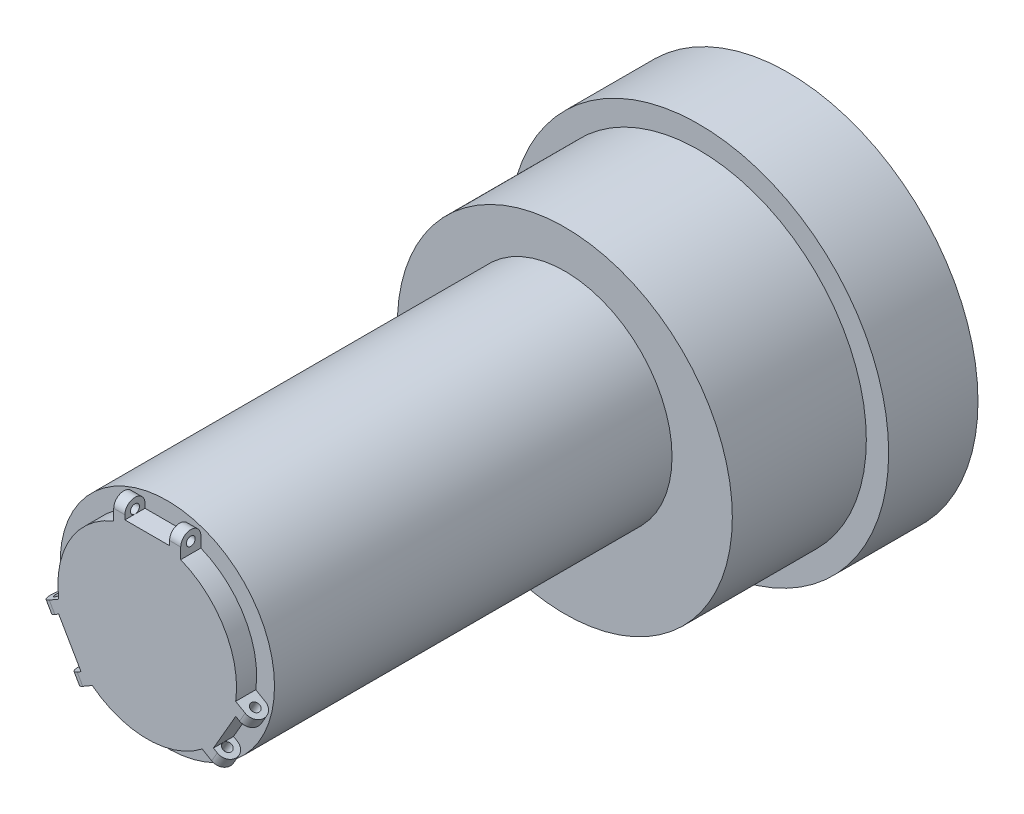
SolidWorks part; units mm, degrees
ref_plane "正面" through (0, 0, 0) normal (0, 0, 1) x (1, 0, 0)
ref_plane "平面" through (0, 0, 0) normal (0, 1, 0) x (1, 0, 0)
ref_plane "右側面" through (0, 0, 0) normal (1, 0, 0) x (0, 0, -1)
sketch "ｽｹｯﾁ1" plane through (0, 0, 0) normal (0, 0, 1) x (1, 0, 0)
  circle A0 centre (0, 0) radius 42.5
  dimension "D1" = 85
extrude "ﾎﾞｽ - 押し出し1" add sketch "ｽｹｯﾁ1" along normal blind 20
sketch "ｽｹｯﾁ2" plane through (0, 0, 20) normal (0, 0, 1) x (1, 0, 0)
  circle A0 centre (0, 0) radius 37.5
  dimension "D1" = 75
extrude "ﾎﾞｽ - 押し出し2" add sketch "ｽｹｯﾁ2" along normal blind 30
sketch "ｽｹｯﾁ3" plane through (0, 0, 50) normal (0, 0, 1) x (1, 0, 0)
  line L0 (0, 5) -> (0, 0) construction
  line L1 (0, 29) -> (0, 37.5) construction
  circle A0 centre (0, 5) radius 24
  circle A1 centre (0, 0) radius 37.5 construction
  dimension "D2" = 48
  dimension "D1" = 8.5
extrude "ﾎﾞｽ - 押し出し3" add sketch "ｽｹｯﾁ3" along normal blind 89
sketch "ｽｹｯﾁ5" plane through (0, 0, 139) normal (0, 0, 1) x (1, 0, 0)
  circle A0 centre (0, 5) radius 20
  circle A1 centre (0, 5) radius 24 construction
  dimension "D1" = 40
extrude "ﾎﾞｽ - 押し出し4" add sketch "ｽｹｯﾁ5" along normal blind 4.5
sketch "Gripper_Direction" plane through (0, 0, 143.5) normal (0, 0, 1) x (1, 0, 0)
  line L0 (-34.641, 25) -> (34.641, 25) construction
  line L1 (34.641, 25) -> (0, -35) construction
  line L2 (0, -35) -> (-34.641, 25) construction
  circle A0 centre (0, 5) radius 20 construction
ref_plane "平面1" through (0, 25, 0) normal (0, 1, 0) x (1, 0, 0)
sketch "ｽｹｯﾁ7" plane through (0, 25, 0) normal (0, 1, 0) x (1, 0, 0)
  line L0 (-20, -139) -> (-20, -143.5) construction
  line L1 (-7.5, -139) -> (7.5, -139)
  line L2 (-7.5, -139) -> (-7.5, -143.5)
  line L3 (-7.5, -143.5) -> (7.5, -143.5)
  line L4 (7.5, -139) -> (7.5, -143.5)
  line L5 (-7.5, -139) -> (7.5, -143.5) construction
  line L6 (-7.5, -143.5) -> (7.5, -139) construction
  line L7 (0, -143.5) -> (-34.641, -143.5) construction
  point P0 (0, -141.25)
  dimension "D1" = 4.5
  dimension "D2" = 20
  dimension "D3" = 15
extrude "ﾎﾞｽ - 押し出し5" add sketch "ｽｹｯﾁ7" against normal blind 10
ref_plane "平面2" through (-15.1554, -8.75, 0) normal (-0.866, -0.5, 0) x (0, 0, 1)
sketch "ｽｹｯﾁ8" plane through (-15.1554, -8.75, 0) normal (-0.866, -0.5, 0) x (0, 0, 1)
  line L1 (139, 11.8301) -> (143.5, 11.8301)
  line L2 (139, 11.8301) -> (139, -3.1699)
  line L3 (139, -3.1699) -> (143.5, -3.1699)
  line L4 (143.5, 11.8301) -> (143.5, -3.1699)
  line L5 (139, 11.8301) -> (143.5, -3.1699) construction
  line L6 (139, -3.1699) -> (143.5, 11.8301) construction
  line L7 (139, -15.6699) -> (143.5, -15.6699) construction
  line L8 (143.5, 38.9711) -> (143.5, 4.3301) construction
  point P0 (141.25, 4.3301)
  dimension "D1" = 20
  dimension "D2" = 15
  dimension "D3" = 4.5
extrude "ﾎﾞｽ - 押し出し6" add sketch "ｽｹｯﾁ8" against normal blind 10
ref_plane "平面3" through (15.1554, -8.75, 0) normal (0.866, -0.5, 0) x (0, 0, -1)
sketch "ｽｹｯﾁ9" plane through (15.1554, -8.75, 0) normal (0.866, -0.5, 0) x (0, 0, -1)
  line L0 (-139, -19.6699) -> (-50, -19.6699) construction
  line L1 (-143.5, 11.8301) -> (-139, 11.8301)
  line L2 (-143.5, 11.8301) -> (-143.5, -3.1699)
  line L3 (-143.5, -3.1699) -> (-139, -3.1699)
  line L4 (-139, 11.8301) -> (-139, -3.1699)
  line L5 (-143.5, 11.8301) -> (-139, -3.1699) construction
  line L6 (-143.5, -3.1699) -> (-139, 11.8301) construction
  line L7 (-143.5, -30.3109) -> (-143.5, 4.3301) construction
  point P0 (-141.25, 4.3301)
  dimension "D1" = 24
  dimension "D2" = 15
  dimension "D3" = 4.5
extrude "ﾎﾞｽ - 押し出し7" add sketch "ｽｹｯﾁ9" against normal blind 10
sketch "ｽｹｯﾁ10" plane through (5.9151, 10.2452, 0) normal (0.5, 0.866, 0) x (0.866, -0.5, 0)
  line L0 (17.5, -143.5) -> (18.5, -143.5)
  line L1 (17.5, -143.5) -> (17.5, -139)
  line L4 (18.5, -143.5) -> (18.5, -139) construction
  line L5 (17.5, -139) -> (18.5, -139)
  arc A3 (18.5, -143.5) -> (18.5, -139) centre (18.5, -141.25) ccw
  dimension "D2" = 1
extrude "ﾎﾞｽ - 押し出し8" add sketch "ｽｹｯﾁ10" against normal blind 15
sketch "ｽｹｯﾁ11" plane through (-7.5, 0, 0) normal (-1, 0, 0) x (0, 0, 1)
  line L0 (139, 25) -> (143.5, 25)
  line L1 (143.5, 25) -> (143.5, 26)
  line L2 (143.5, 26) -> (139, 26) construction
  line L3 (139, -19) -> (139, 29) construction
  line L4 (139, 26) -> (139, 25)
  arc A0 (143.5, 26) -> (139, 26) centre (141.25, 26) ccw
  dimension "D1" = 1
extrude "ﾎﾞｽ - 押し出し9" add sketch "ｽｹｯﾁ11" against normal blind 15
sketch "ｽｹｯﾁ12" plane through (1.5849, -2.7452, 0) normal (0.5, -0.866, 0) x (0.866, 0.5, 0)
  line L0 (-17.5, 139) -> (-17.5, 143.5)
  line L1 (-17.5, 143.5) -> (-18.5, 143.5)
  line L2 (-18.5, 143.5) -> (-18.5, 139) construction
  line L3 (26.5, 139) -> (-21.5, 139) construction
  line L4 (-18.5, 139) -> (-17.5, 139)
  arc A0 (-18.5, 143.5) -> (-18.5, 139) centre (-18.5, 141.25) ccw
  dimension "D1" = 1
extrude "ﾎﾞｽ - 押し出し10" add sketch "ｽｹｯﾁ12" against normal blind 15
sketch "ｽｹｯﾁ13" plane through (-7.5, 0, 0) normal (-1, 0, 0) x (0, 0, 1)
  circle A0 centre (141.25, 26) radius 1
  arc A1 (143.5, 26) -> (139, 26) centre (141.25, 26) ccw construction
  dimension "D1" = 2
extrude "ｶｯﾄ - 押し出し1" cut sketch "ｽｹｯﾁ13" against normal through all
sketch "ｽｹｯﾁ14" plane through (1.5849, -2.7452, 0) normal (0.5, -0.866, 0) x (-0.866, -0.5, 0)
  circle A0 centre (18.5, -141.25) radius 1
  arc A1 (18.5, -143.5) -> (18.5, -139) centre (18.5, -141.25) ccw construction
  dimension "D1" = 2
extrude "ｶｯﾄ - 押し出し2" cut sketch "ｽｹｯﾁ14" against normal through all
sketch "ｽｹｯﾁ15" plane through (5.9151, 10.2452, 0) normal (0.5, 0.866, 0) x (0.866, -0.5, 0)
  circle A0 centre (18.5, -141.25) radius 1
  arc A1 (18.5, -143.5) -> (18.5, -139) centre (18.5, -141.25) ccw construction
  dimension "D1" = 2
extrude "ｶｯﾄ - 押し出し3" cut sketch "ｽｹｯﾁ15" against normal through all
sketch "ｽｹｯﾁ16" plane through (0, 0, 143.5) normal (0, 0, 1) x (1, 0, 0)
  line L0 (-21.9365, 0.9952) -> (-14.4365, -11.9952) construction
  circle A0 centre (0, 5) radius 21 construction
ref_plane "平面4" through (0, 28.25, 0) normal (0, 1, 0) x (1, 0, 0)
ref_plane "平面5" through (-17.97, -10.375, 0) normal (-0.866, -0.5, 0) x (0, 0, 1)
ref_plane "平面6" through (17.97, -10.375, 0) normal (0.866, -0.5, 0) x (0, 0, -1)
sketch "ｽｹｯﾁ18" plane through (-17.97, -10.375, 0) normal (-0.866, -0.5, 0) x (0, 0, 1)
  line L1 (139, 9.3301) -> (143.5, 9.3301)
  line L2 (139, 9.3301) -> (139, -0.6699)
  line L3 (139, -0.6699) -> (143.5, -0.6699)
  line L4 (143.5, 9.3301) -> (143.5, -0.6699)
  line L5 (139, 9.3301) -> (143.5, -0.6699) construction
  line L6 (139, -0.6699) -> (143.5, 9.3301) construction
  line L7 (139, 28.3301) -> (50, 28.3301) construction
  line L8 (143.5, 11.8301) -> (143.5, -3.1699) construction
  point P0 (141.25, 4.3301)
  dimension "D1" = 24
  dimension "D2" = 4.5
  dimension "D3" = 10
extrude "ｶｯﾄ - 押し出し4" cut sketch "ｽｹｯﾁ18" against normal blind 3.25
sketch "ｽｹｯﾁ19" plane through (17.97, -10.375, 0) normal (0.866, -0.5, 0) x (0, 0, -1)
  line L0 (-139, -19.6699) -> (-50, -19.6699) construction
  line L1 (-139, 9.3301) -> (-143.5, 9.3301)
  line L2 (-139, 9.3301) -> (-139, -0.6699)
  line L3 (-139, -0.6699) -> (-143.5, -0.6699)
  line L4 (-143.5, 9.3301) -> (-143.5, -0.6699)
  line L5 (-139, 9.3301) -> (-143.5, -0.6699) construction
  line L6 (-139, -0.6699) -> (-143.5, 9.3301) construction
  line L7 (-143.5, -3.1699) -> (-143.5, 11.8301) construction
  point P0 (-141.25, 4.3301)
  dimension "D1" = 24
  dimension "D2" = 10
  dimension "D3" = 4.5
extrude "ｶｯﾄ - 押し出し5" cut sketch "ｽｹｯﾁ19" against normal blind 3.25
sketch "ｽｹｯﾁ20" plane through (0, 28.25, 0) normal (0, 1, 0) x (1, 0, 0)
  line L0 (24, -139) -> (24, -50) construction
  line L1 (-5, -139) -> (5, -139)
  line L2 (-5, -139) -> (-5, -143.5)
  line L3 (-5, -143.5) -> (5, -143.5)
  line L4 (5, -139) -> (5, -143.5)
  line L5 (-5, -139) -> (5, -143.5) construction
  line L6 (-5, -143.5) -> (5, -139) construction
  line L7 (7.5, -143.5) -> (-7.5, -143.5) construction
  point P0 (0, -141.25)
  dimension "D1" = 24
  dimension "D2" = 4.5
  dimension "D3" = 10
extrude "ｶｯﾄ - 押し出し6" cut sketch "ｽｹｯﾁ20" against normal blind 3.25
sketch "ｽｹｯﾁ21" plane through (0, 0, 0) normal (0, 0, -1) x (-1, 0, 0)
  point P0 (0, 0)
sketch3d "3Dｽｹｯﾁ1"
  line L0 (0, 0, 0) -> (0, 30, 0)
  line L1 (0, 0, 0) -> (-30, 0, 0)
  line L2 (0, 0, 0) -> (0, 0, 30)
  dimension "D1" = 30
  dimension "D2" = 30
  dimension "D3" = 30
